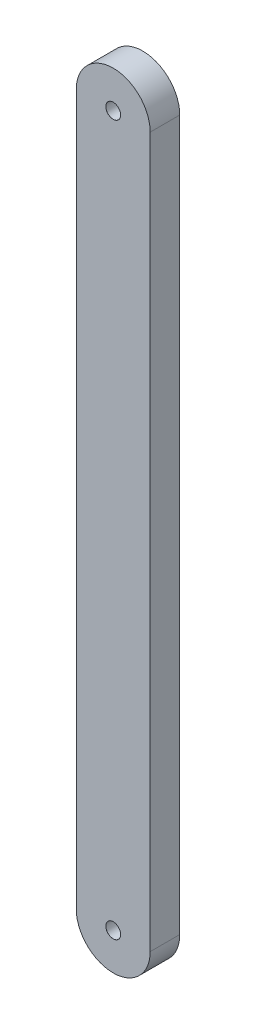
SolidWorks part; units mm, degrees
material "Alloy Steel"
ref_plane "Front Plane" through (0, 0, 0) normal (0, 0, 1) x (1, 0, 0)
ref_plane "Top Plane" through (0, 0, 0) normal (0, 1, 0) x (1, 0, 0)
ref_plane "Right Plane" through (0, 0, 0) normal (1, 0, 0) x (0, 0, -1)
sketch "Sketch2" plane through (0, 0, 0) normal (0, 0, 1) x (1, 0, 0)
  line L0 (-50, -240) -> (-50, 240)
  line L1 (0, 240) -> (0, -240)
  arc A0 (-50, 240) -> (0, 240) centre (-25, 240) cw
  arc A1 (0, -240) -> (-50, -240) centre (-25, -240) cw
  dimension "D1" = 480
  dimension "D2" = 50
extrude "Boss-Extrude1" add sketch "Sketch2" along normal blind 20
hole_wizard "Ø10.0mm Dowel Hole1" positions "Sketch3" profile "Sketch4" hole size "Ø10.0" standard "ANSI Metric" end condition through all
sketch "Sketch3" plane through (0, 0, 20) normal (0, 0, 1) x (1, 0, 0)
  point P0 (-25, 240)
  point P3 (-25, -240)
sketch "Sketch4" plane through (-25, 240, 20) normal (1, 0, 0) x (0, -1, 0)
  line L0 (0, 0) -> (0, 20)
  line L1 (0, 20) -> (5, 20)
  line L2 (5, 20) -> (5, 0.025)
  line L3 (5, 0.025) -> (5.025, 0)
  line L5 (5.025, 0) -> (0, 0)
  line L6 (-5, 0.025) -> (-5.025, 0) construction
  line L11 (0, -6.35) -> (0, 107.95) construction
  dimension "Thru Hole Dia." = 10
  dimension "Thru Hole Depth" = 20
  dimension "Near C'Sink Dia." = 10.05
  dimension "Near C'Sink Angle" = 90
scale "Scale1" scale about centroid uniform scaling yes scale factor 0.125
